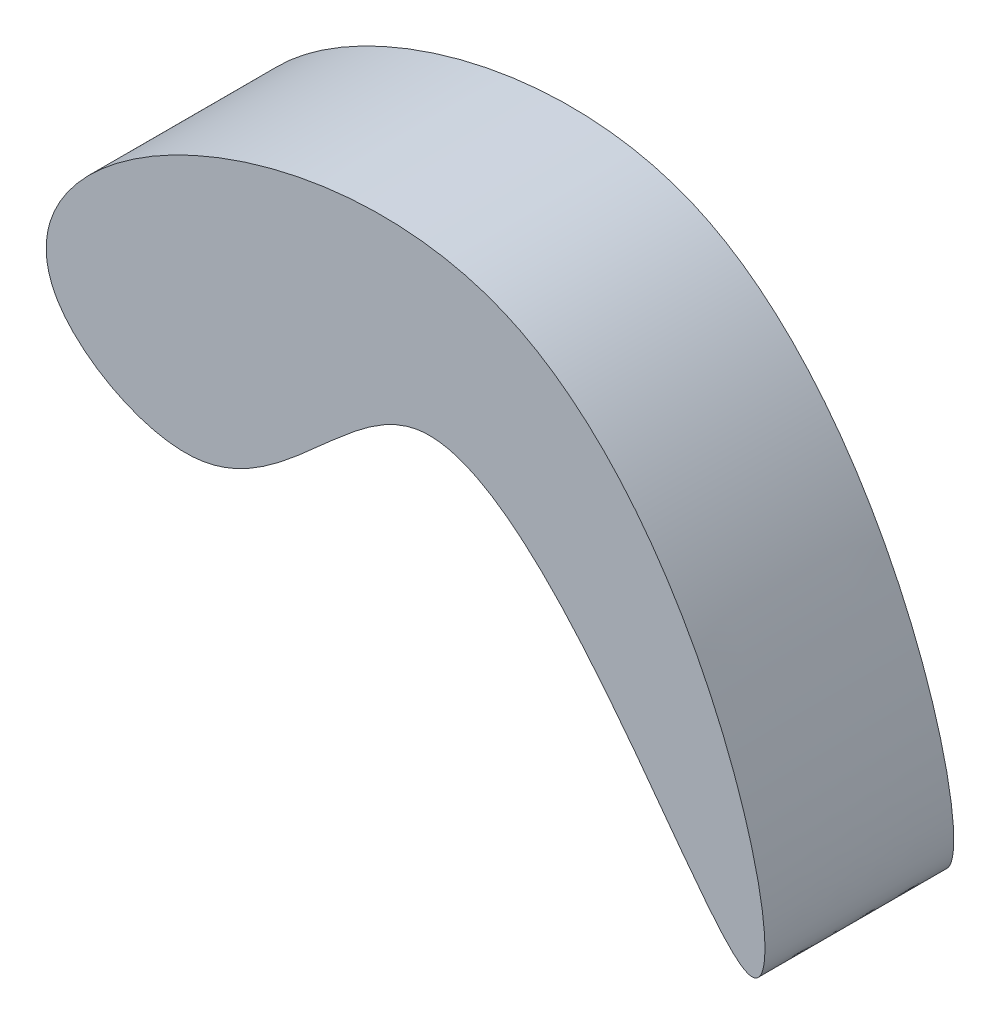
SolidWorks part; units mm, degrees
ref_plane "Front Plane" through (0, 0, 0) normal (0, 0, 1) x (1, 0, 0)
ref_plane "Top Plane" through (0, 0, 0) normal (0, 1, 0) x (1, 0, 0)
ref_plane "Right Plane" through (0, 0, 0) normal (1, 0, 0) x (0, 0, -1)
sketch "Sketch1" plane through (0, 0, 0) normal (0, 0, 1) x (1, 0, 0)
  spline S0 degree 3 poles (20.7569, 11.5809) (-12.2238, 29.5184) (55.2871, 66.6804) (77.5983, -28.8795) (39.2453, 47.1043) (20.7569, 11.5809) (-12.2238, 29.5184) (55.2871, 66.6804) knots -0.462196 -0.222276 -0.081471 0 0.264443 0.537804 0.777724 0.918529 1 1.264443 1.537804 1.777724 only from (3.5666, 23.2195) to (3.5666, 23.2195)
extrude "Boss-Extrude1" add sketch "Sketch1" along normal blind 7 and the other way blind 10
